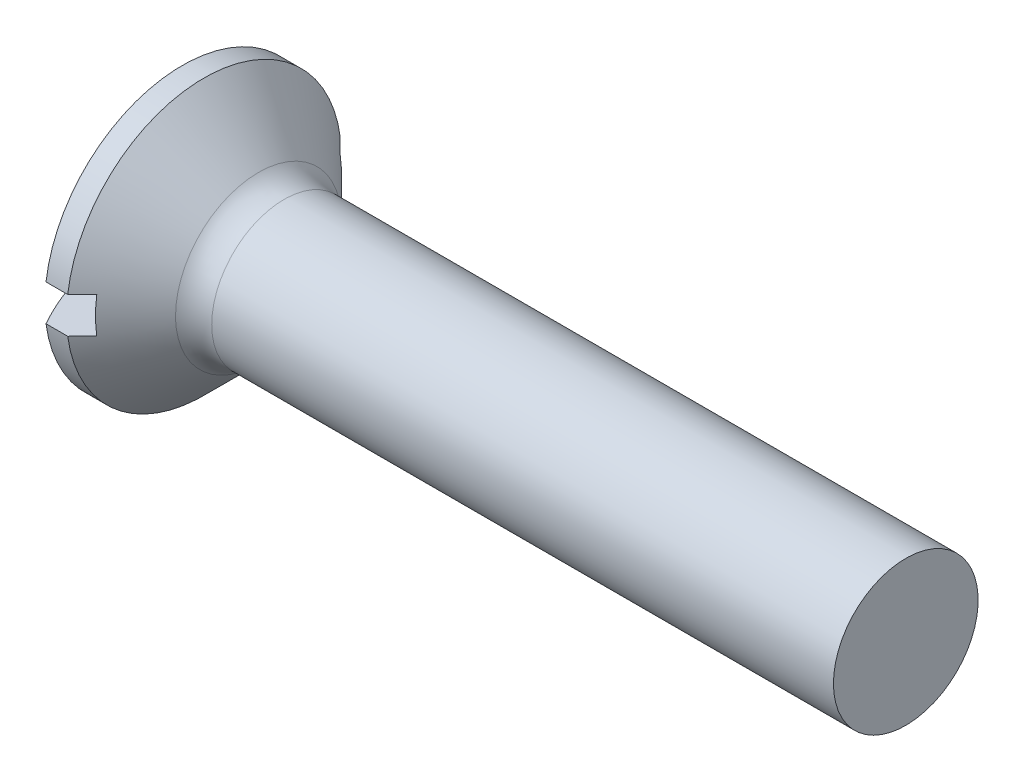
SolidWorks part; units mm, degrees
ref_plane "Plane1" through (0, 0, 0) normal (0, 0, 1) x (1, 0, 0)
ref_plane "Plane2" through (0, 0, 0) normal (0, 1, 0) x (1, 0, 0)
ref_plane "Plane3" through (0, 0, 0) normal (1, 0, 0) x (0, 0, -1)
sketch "BodySke" plane through (0, 0, 0) normal (0, 0, 1) x (1, 0, 0)
  line L0 (0, 0) -> (10.5, 0)
  line L1 (10.5, 0) -> (10.5, 1)
  line L2 (10.5, 1) -> (1.7, 1)
  line L3 (0.8, -1.9) -> (1.7, -1) construction
  line L4 (-15.875, 0) -> (82.55, 0) construction
  line L5 (0.8, 1.9) -> (1.7, 1)
  line L6 (2.1, 4.175) -> (2.1, -11.7) construction
  line L7 (0.5, 2.7793) -> (0.5, -13.0957) construction
  line L8 (0.8, 1.9) -> (0.5, 1.9)
  arc A0 (0, 0) -> (0.5, 1.9) centre (3.86, 0) cw
  dimension "Head_ang" = 90
  dimension "Diameter" = 2
  dimension "Advance" = 0.4
  dimension "Thread_nom" = 10
  dimension "Oval_ht" = 0.5
  dimension "Side_ht" = 1.2
  dimension "Head_dia" = 3.8
  dimension "Length" = 10
revolve "Base-Revolve" add sketch "BodySke"
cosmetic thread "ThreadCosmetic"
extrude "Slot" cut sketch "Sketch2" along normal blind 1
sketch "Sketch2" plane through (0, 0, 0) normal (1, 0, 0) x (0, 0, -1)
  line L0 (1.9, -0.25) -> (-1.9, -0.25)
  line L1 (1.9, -0.25) -> (1.9, 0.25)
  line L2 (-1.9, 0.25) -> (1.9, 0.25)
  line L3 (-1.9, 0.25) -> (-1.9, -0.25)
  dimension "D1" = 3.8
  dimension "Slot_width" = 0.5
  dimension "D3" = 1.9
  dimension "D4" = 0.25
fillet "Fillet1" radius 0.5 1 edges at (1.7, 0, 1)
sketch "ThdSchSke" plane through (0, 0, 0) normal (0, 0, 1) x (1, 0, 0)
  line L0 (2.1, -0.774) -> (1.9418, -1)
  line L1 (2.1, -0.774) -> (2.2582, -1)
  line L2 (2.2582, -1) -> (2.2582, -1.25)
  line L3 (-3.175, 0) -> (5.1513, 0) construction
  line L5 (2.2582, -1.25) -> (1.9418, -1.25)
  line L6 (1.9418, -1.25) -> (1.9418, -1)
  dimension "Diameter" = 2
  dimension "SideAngle" = 55
  dimension "VeeAngle" = 70
  dimension "Thread_minor" = 1.548
  dimension "Overcut" = 2.5
  dimension "Start" = 2.1
revolve "ThreadSchematic" [suppressed] cut sketch "ThdSchSke" angle 360 about L3
pattern_linear "ThdSchPat" [suppressed]
equation "\"D1@Sketch2\" = \"Head_dia@BodySke\""
equation "\"D3@Sketch2\" = \"D1@Sketch2\" / 2"
equation "\"D4@Sketch2\" = \"Slot_width@Sketch2\" / 2"
equation "\"Thread_length@ThreadCosmetic\" = ((sgn( (\"Length@BodySke\" - \"Advance@BodySke\" - \"Side_ht@BodySke\" ) - \"Thread_nom@BodySke\" )-1)*( (\"Length@BodySke\" - \"Advance@BodySke\" - \"Side_ht@BodySke\" ) - \"Thread_nom@BodySke\" ))/-2+ \"Thread_nom@BodySke\""
equation "\"Thread_minor@ThdSchSke\" = \"Thread_minor@ThreadCosmetic\""
equation "\"Diameter@ThdSchSke\" = \"Diameter@BodySke\""
equation "\"Overcut@ThdSchSke\" = \"Diameter@BodySke\" * 1.25"
equation "\"Start@ThdSchSke\" = \"Oval_ht@BodySke\" + \"Length@BodySke\" - \"Thread_length@ThreadCosmetic\"  '---Countersunk---"
equation "\"Num_threads@ThdSchPat\" = int( \"Thread_length@ThreadCosmetic\" / \"Advance@BodySke\" + 0.999 )  + 1"
equation "\"Advance@ThdSchPat\" = \"Thread_length@ThreadCosmetic\" /  (\"Num_threads@ThdSchPat\" - 1) 'relax it"
